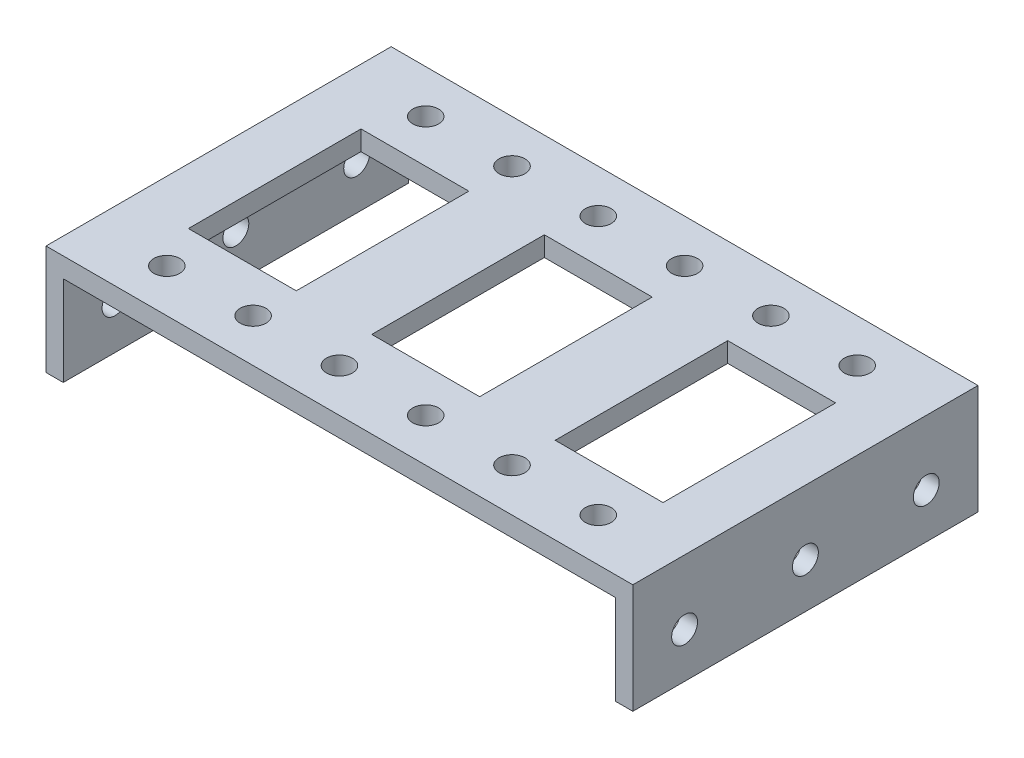
SolidWorks part; units mm, degrees
material "7075-O (SS)"
ref_plane "Front Plane" through (0, 0, 0) normal (0, 0, 1) x (1, 0, 0)
ref_plane "Top Plane" through (0, 0, 0) normal (0, 1, 0) x (1, 0, 0)
ref_plane "Right Plane" through (0, 0, 0) normal (1, 0, 0) x (0, 0, -1)
sketch "Sketch1" plane through (0, 0, 0) normal (0, 0, 1) x (1, 0, 0)
  line L0 (0, 0) -> (0, 38.1127) construction
  line L1 (-34, 0) -> (-34, 12.7)
  line L2 (-34, 12.7) -> (34, 12.7)
  line L3 (-34, 0) -> (-32, 0)
  line L4 (-32, 0) -> (-32, 10.414)
  line L5 (-32, 10.414) -> (32, 10.414)
  line L6 (32, 0) -> (32, 10.414)
  line L7 (34, 0) -> (32, 0)
  line L8 (34, 0) -> (34, 12.7)
  point P10 (0, 10.414)
  point P13 (0, 12.7)
  dimension "D1" = 68
  dimension "D2" = 2
  dimension "D3" = 2.286
  dimension "D4" = 12.7
extrude "Boss-Extrude1" add sketch "Sketch1" along normal mid plane 40 contours L2 L8 L7 L6 L5 L4 L3 L1
sketch "Sketch4" plane through (34, 0, 0) normal (1, 0, 0) x (0, 0, -1)
  line L0 (0, 0) -> (0, 11.3278) construction
  line L2 (-20, 12.7) -> (20, 12.7) construction
  point P0 (-14, 5.207)
  point P1 (0, 5.207)
  point P8 (14, 5.207)
  dimension "D1" = 7.493
  dimension "D2" = 28
hole_wizard "Ø3.0mm Dowel Hole1" positions "Sketch5" profile "Sketch6" hole size "Ø3.0" standard "ANSI Metric" end condition through all
sketch "Sketch5" plane through (34, 0, 0) normal (1, 0, 0) x (0, 0, -1)
  point P0 (-14, 5.207)
  point P3 (14, 5.207)
  point P6 (0, 5.207)
sketch "Sketch6" plane through (34, 5.207, 14) normal (0, 1, 0) x (0, 0, -1)
  line L0 (0, 0) -> (0, 68)
  line L1 (0, 68) -> (1.5, 68)
  line L2 (1.5, 68) -> (1.5, 0)
  line L5 (1.5, 0) -> (0, 0)
  line L11 (0, -6.35) -> (0, 107.95) construction
  dimension "Thru Hole Dia." = 3
  dimension "Thru Hole Depth" = 68
sketch "Sketch7" plane through (0, 12.7, 0) normal (0, 1, 0) x (1, 0, 0)
  line L0 (-34, -20) -> (34, -20) construction
  line L1 (-34, 0) -> (41.1087, 0) construction
  line L2 (-34, -20) -> (-34, 20) construction
  line L3 (0, 0) -> (0, 33.4726) construction
  line L4 (0, 33.4726) -> (-4.0368, 29.4358) construction
  line L5 (-4.0368, 29.4358) -> (-3.9306, 28.9981) construction
  point P0 (25, -15)
  point P1 (15, -15)
  point P2 (5, -15)
  point P11 (5, 15)
  point P12 (15, 15)
  point P13 (25, 15)
  dimension "D1" = 10
  dimension "D2" = 5
  dimension "D3" = 5
  dimension "D4" = 5
  dimension "D5" = 10
  dimension "D6" = 10
hole_wizard "Ø3.0mm Dowel Hole2" positions "Sketch8" profile "Sketch9" hole size "Ø3.0" standard "ANSI Metric" end condition through all
sketch "Sketch8" plane through (0, 12.7, 0) normal (0, 1, 0) x (1, 0, 0)
  point P0 (25, -15)
  point P3 (15, -15)
  point P6 (5, -15)
  point P9 (25, 15)
  point P12 (15, 15)
  point P15 (5, 15)
sketch "Sketch9" plane through (25, 12.7, 15) normal (1, 0, 0) x (0, 0, 1)
  line L0 (0, 0) -> (0, 12.7)
  line L1 (0, 12.7) -> (1.5, 12.7)
  line L2 (1.5, 12.7) -> (1.5, 0)
  line L5 (1.5, 0) -> (0, 0)
  line L11 (0, -6.35) -> (0, 107.95) construction
  dimension "Thru Hole Dia." = 3
  dimension "Thru Hole Depth" = 12.7
sketch "Sketch10" plane through (0, 12.7, 0) normal (0, 1, 0) x (1, 0, 0)
  line L0 (0, 0) -> (0, -42.9836) construction
  line L1 (0, 0) -> (-36.8596, 0) construction
  line L3 (-27.5, -10) -> (-15, -10)
  line L4 (-27.5, -10) -> (-27.5, 10)
  line L5 (-27.5, 10) -> (-15, 10)
  line L6 (-15, -10) -> (-15, 10)
  dimension "D1" = 55
  dimension "D2" = 15
  dimension "D3" = 20
extrude "Cut-Extrude1" cut sketch "Sketch10" against normal blind 10
mirror "Mirror1" about plane through (0, 0, 0) normal (1, 0, 0) of "Cut-Extrude1"
sketch "Sketch11" plane through (0, 12.7, 0) normal (0, 1, 0) x (1, 0, 0)
  line L0 (0, 0) -> (-20.0399, 0) construction
  line L1 (-6.25, -10) -> (6.25, -10)
  line L2 (-6.25, -10) -> (-6.25, 10)
  line L3 (-6.25, 10) -> (6.25, 10)
  line L4 (6.25, -10) -> (6.25, 10)
  line L5 (-34, 0) -> (41.1087, 0) construction
  line L6 (0, 0) -> (0, 30.5246) construction
  line L7 (-15, 10) -> (-27.5, 10) construction
  line L8 (-27.5, -10) -> (-15, -10) construction
extrude "Cut-Extrude2" cut sketch "Sketch11" against normal blind 10
mirror "Mirror2" about plane through (0, 0, 0) normal (1, 0, 0) of "Ø3.0mm Dowel Hole2"
